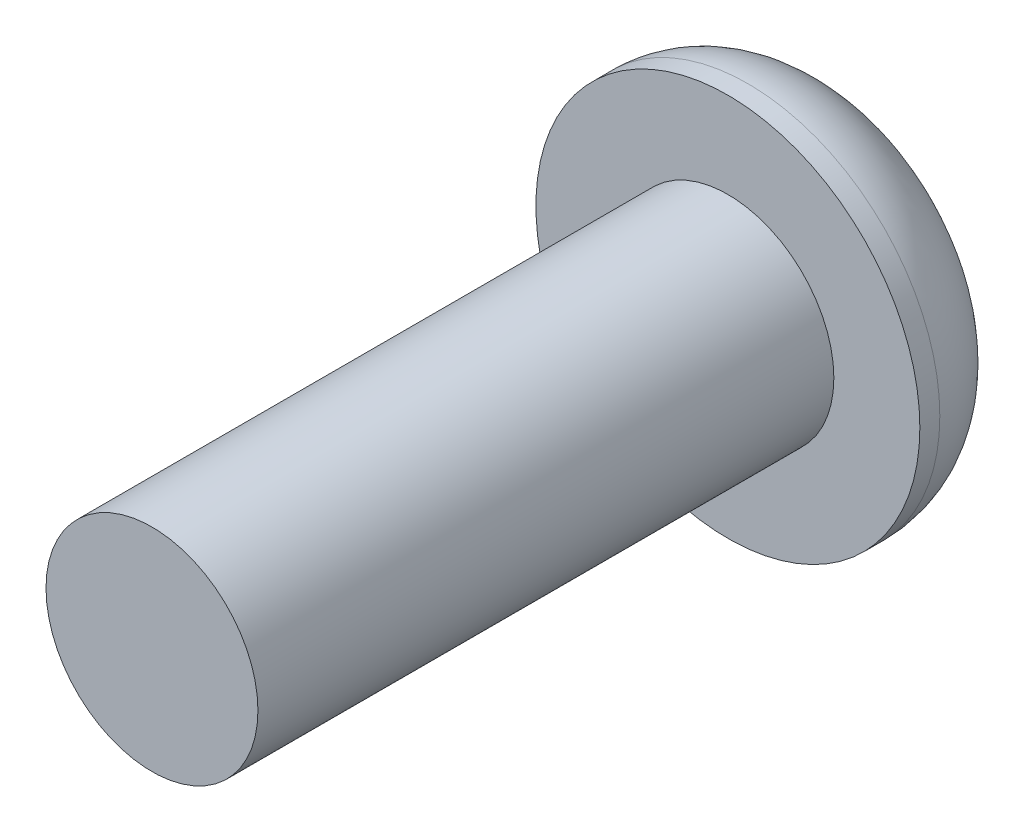
SolidWorks part; units mm, degrees
ref_plane "Front Plane" through (0, 0, 0) normal (0, 0, 1) x (1, 0, 0)
ref_plane "Top Plane" through (0, 0, 0) normal (0, 1, 0) x (1, 0, 0)
ref_plane "Right Plane" through (0, 0, 0) normal (1, 0, 0) x (0, 0, -1)
sketch "Sketch1" plane through (0, 0, 0) normal (0, 0, 1) x (1, 0, 0)
  circle A0 centre (0, 0) radius 3.175
  dimension "D1" = 6.35
extrude "Extrude1" add sketch "Sketch1" along normal blind 1.8542
fillet "Fillet1" radius 1.524 1 edges at (3.175, 0, 0)
sketch "Sketch2" plane through (0, 0, 1.8542) normal (0, 0, 1) x (1, 0, 0)
  circle A0 centre (0, 0) radius 1.7526
  dimension "D1" = 3.5052
extrude "Extrude2" add sketch "Sketch2" along normal blind 9.525
sketch "Sketch3" plane through (0, 0, 0) normal (0, 0, -1) x (-1, 0, 0)
  line L1 (0.5909, 0.9816) -> (-0.5546, 1.0025)
  line L3 (-0.5546, 1.0025) -> (-1.1455, 0.0209)
  line L5 (-1.1455, 0.0209) -> (-0.5909, -0.9816)
  line L6 (-0.5909, -0.9816) -> (0.5546, -1.0025)
  line L7 (0.5546, -1.0025) -> (1.1455, -0.0209)
  line L8 (1.1455, -0.0209) -> (0.5909, 0.9816)
  circle A1 centre (0, 0) radius 0.9922 construction
  point P0 (0, 0)
  point P8 (0, 0)
extrude "Extrude3" cut sketch "Sketch3" against normal blind 1.016
